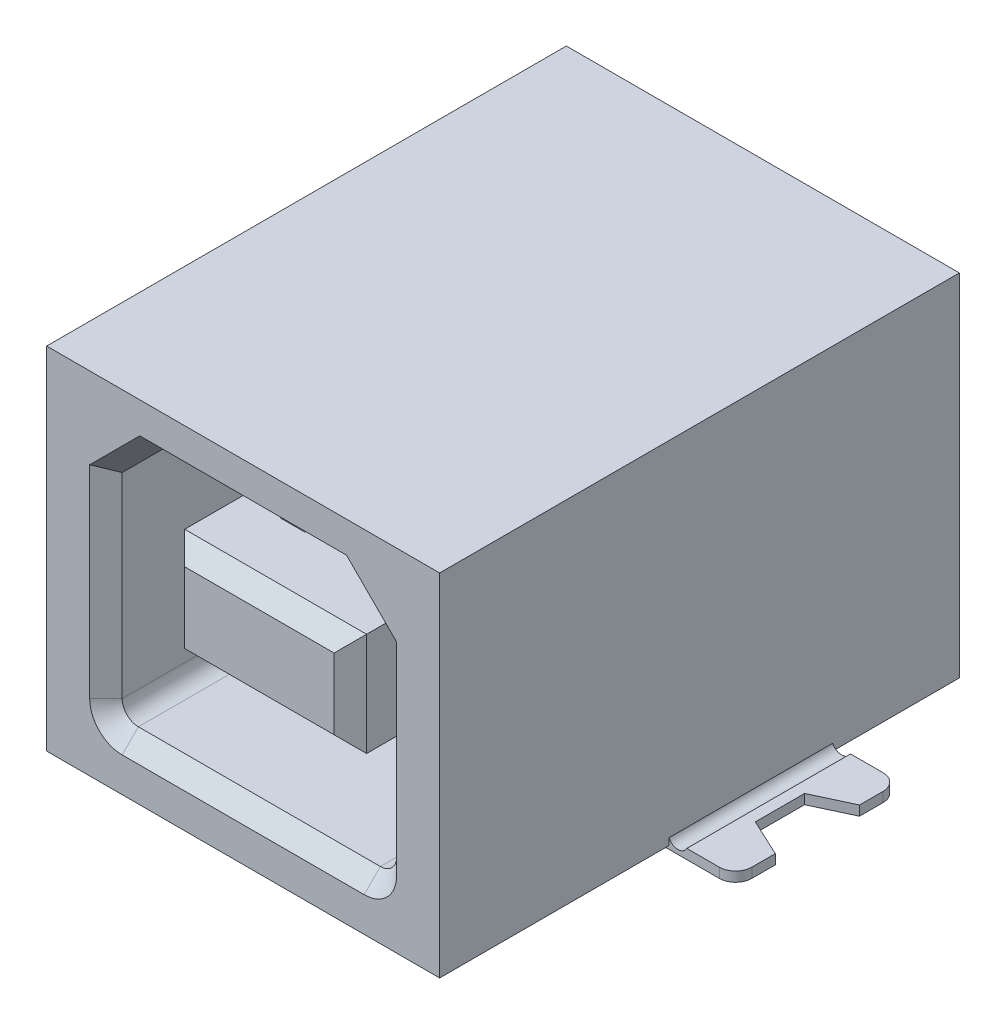
SolidWorks part; units mm, degrees
ref_plane "Front" through (0, 0, 0) normal (0, 0, 1) x (1, 0, 0)
ref_plane "Top" through (0, 0, 0) normal (0, 1, 0) x (1, 0, 0)
ref_plane "Right" through (0, 0, 0) normal (1, 0, 0) x (0, 0, -1)
sketch "Sketch1" plane through (0, 0, 0) normal (0, 0, 1) x (1, 0, 0)
  line L0 (-6.05, 5.4) -> (6.05, -5.4) construction
  line L1 (-6.05, 5.4) -> (6.05, 5.4)
  line L2 (-6.05, 5.4) -> (-6.05, -5.4)
  line L3 (-6.05, -5.4) -> (6.05, -5.4)
  line L4 (6.05, 5.4) -> (6.05, -5.4)
  dimension "D1" = 12.1
  dimension "D2" = 10.8
extrude "Base" add sketch "Sketch1" along normal mid plane 16
sketch "Sketch2" plane through (0, 0, 8) normal (0, 0, 1) x (1, 0, 0)
  line L0 (-2.975, 3.94) -> (-4.225, 2.69)
  line L1 (3.725, -3.84) -> (-3.725, -3.84)
  line L2 (4.225, -3.34) -> (4.225, 2.69)
  line L3 (2.975, 3.94) -> (-2.975, 3.94)
  line L4 (-4.225, -3.34) -> (-4.225, 2.69)
  line L5 (4.225, 2.69) -> (2.975, 3.94)
  line L6 (4.225, 3.94) -> (-4.225, -3.84) construction
  line L7 (6.05, 5.4) -> (-6.05, 5.4) construction
  line L9 (0, 0.05) -> (13.9883, 0.05) construction
  arc A0 (-3.725, -3.84) -> (-4.225, -3.34) centre (-3.725, -3.34) cw
  arc A1 (3.725, -3.84) -> (4.225, -3.34) centre (3.725, -3.34) ccw
  point P1 (4.225, 3.94)
  point P2 (-4.225, 3.94)
  point P12 (-4.225, -3.84)
  dimension "D1" = 0.5
  dimension "D2" = 5.35
  dimension "D3" = 8.45
  dimension "D5" = 7.78
extrude "Contact Opening" cut sketch "Sketch2" against normal blind 9
chamfer "Contact Opening Lead-in" distance 0.5 angle 45 8 edges at (-3.6, 3.315, 8) (0, 3.94, 8) (3.6, 3.315, 8) (4.225, -0.325, 8) (4.0786, -3.6936, 8) (0, -3.84, 8) (-4.0786, -3.6936, 8) (-4.225, -0.325, 8)
sketch "Sketch3" plane through (0, 0, -1) normal (0, 0, 1) x (1, 0, 0)
  line L0 (-2.8, 1.64) -> (2.8, -1.54) construction
  line L1 (-2.8, 1.64) -> (2.8, 1.64)
  line L2 (-2.8, 1.64) -> (-2.8, -1.54)
  line L3 (-2.8, -1.54) -> (2.8, -1.54)
  line L4 (2.8, 1.64) -> (2.8, -1.54)
  line L5 (-2.8, 0.05) -> (2.8, 0.05) construction
  line L6 (6.05, 5.4) -> (-6.05, 5.4) construction
  dimension "D1" = 5.6
  dimension "D2" = 3.18
  dimension "D3" = 5.35
extrude "Contact Area" add sketch "Sketch3" along normal blind 8.5
chamfer "Contact Area Lead-in" distance 0.5 angle 45 4 edges at (0, 1.64, 7.5) (2.8, 0.05, 7.5) (0, -1.54, 7.5) (-2.8, 0.05, 7.5)
ref_plane "Ground Leg Plane" through (0, 0, -1.58) normal (0, 0, 1) x (1, 0, 0)
sketch "Sketch4" plane through (0, 0, -1.58) normal (0, 0, 1) x (1, 0, 0)
  line L0 (0, 0) -> (0, -12.5407) construction
  line L1 (6.02, -5.058) -> (5.72, -5.1007)
  line L2 (6.5995, -5.2) -> (8.1, -5.2)
  line L3 (8.1, -5.2) -> (8.1, -5.5)
  line L5 (-5.9087, -5.5) -> (-8.1, -5.5)
  line L6 (-8.1, -5.2) -> (-8.1, -5.5)
  line L7 (-6.5995, -5.2) -> (-8.1, -5.2)
  line L8 (-6.02, -5.058) -> (-5.72, -5.1007)
  line L9 (5.9087, -5.5) -> (8.1, -5.5)
  arc A0 (6.02, -5.058) -> (6.5995, -5.2) centre (6.3271, -5.058) ccw
  arc A1 (-5.72, -5.1007) -> (-5.9087, -5.5) centre (-6.3271, -5.058) cw
  arc A2 (-6.02, -5.058) -> (-6.5995, -5.2) centre (-6.3271, -5.058) cw
  arc A5 (5.72, -5.1007) -> (5.9087, -5.5) centre (6.3271, -5.058) ccw
  dimension "D2" = 8.1
  dimension "D3" = 0.3
  dimension "D1" = 10.6
extrude "Ground Legs" add sketch "Sketch4" along normal mid plane 5.04
sketch "Sketch9" plane through (0, -5.2, 0) normal (0, 1, 0) x (-1, 0, 0)
  line L0 (-8.1, -4.1) -> (-8.1, -3.6)
  line L2 (-8.1, -4.1) -> (-7.6, -4.1)
  line L4 (0, -1.58) -> (-12.8295, -1.58) construction
  line L5 (-8.1, -2.8759) -> (-6.9467, -2.3383)
  line L6 (-8.1, 0.94) -> (-8.1, -4.1) construction
  line L7 (-6.9467, -2.3383) -> (-6.9467, -0.8217)
  line L8 (-8.1, -2.8759) -> (-8.1, -0.2841)
  line L9 (-8.1, -0.2841) -> (-6.9467, -0.8217)
  line L10 (-8.1, 0.94) -> (-7.6, 0.94)
  line L11 (-8.1, 0.94) -> (-8.1, 0.44)
  line L12 (6.321, -1.58) -> (-6.321, -1.58) construction
  line L13 (0, 0) -> (0, 10.0194) construction
  line L14 (8.1, 0.94) -> (8.1, 0.44)
  line L15 (8.1, 0.94) -> (7.6, 0.94)
  line L16 (8.1, -0.2841) -> (6.9467, -0.8217)
  line L17 (8.1, -2.8759) -> (8.1, -0.2841)
  line L18 (6.9467, -2.3383) -> (6.9467, -0.8217)
  line L19 (8.1, -2.8759) -> (6.9467, -2.3383)
  line L20 (8.1, -4.1) -> (7.6, -4.1)
  line L21 (8.1, -4.1) -> (8.1, -3.6)
  arc A0 (-8.1, -3.6) -> (-7.6, -4.1) centre (-7.6, -3.6) ccw
  arc A1 (-8.1, 0.44) -> (-7.6, 0.94) centre (-7.6, 0.44) cw
  arc A2 (8.1, 0.44) -> (7.6, 0.94) centre (7.6, 0.44) ccw
  arc A3 (8.1, -3.6) -> (7.6, -4.1) centre (7.6, -3.6) cw
  point P10 (-8.1, -4.1)
  point P17 (-8.1, 0.94)
  point P19 (-8.1, -1.58)
  point P20 (-6.9467, -1.58)
  point P32 (6.9467, -1.58)
  point P33 (8.1, -1.58)
  point P34 (8.1, 0.94)
  point P35 (8.1, -4.1)
  dimension "D1" = 0.5
  dimension "D2" = 0.5
  dimension "D3" = 1.2959
  dimension "D4" = 0.7583
extrude "ground legs shape" cut sketch "Sketch9" against normal blind 0.3
ref_plane "Tail Plane" through (0, 0, -6.9) normal (0, 0, -1) x (-1, 0, 0)
ref_plane "Contact Plane" through (-1.25, 0, 0) normal (1, 0, 0) x (0, 0, -1)
ref_plane "SM TAILS PLANE" through (0.75, 0, 0) normal (1, 0, 0) x (0, 0, -1)
sketch "Sketch11" plane through (0.75, 0, 0) normal (1, 0, 0) x (0, 0, -1)
  line L1 (7.15, -5.3) -> (7.15, -5.15)
  line L2 (7.15, -5.15) -> (7.4, -5.15)
  line L3 (8, -5.4) -> (8, 5.4) construction
  line L4 (4.1, -5.4) -> (8, -5.4) construction
  line L5 (-0.94, -5.5) -> (4.1, -5.5) construction
  line L6 (7.5, -5.25) -> (9.15, -5.25)
  line L8 (7.35, -5.5) -> (9.15, -5.5)
  line L9 (9.15, -5.25) -> (9.15, -5.5)
  arc A0 (7.4, -5.15) -> (7.5, -5.25) centre (7.5, -5.15) ccw
  arc A1 (7.15, -5.3) -> (7.35, -5.5) centre (7.35, -5.3) ccw
  dimension "D2" = 0.1
  dimension "D3" = 1.15
  dimension "D6" = 0.2
  dimension "D1" = 0.25
  dimension "D4" = 0.25
  dimension "D5" = 0.15
  dimension "D7" = 0.25
  dimension "D8" = 0.85
extrude "SM Tails" add sketch "Sketch11" along normal mid plane 0.6
sketch "Sketch8" plane through (-1.25, 0, 0) normal (1, 0, 0) x (0, 0, -1)
  line L0 (1, 1.64) -> (-2.5111, 2.2199)
  line L1 (-4.0305, 2.0775) -> (-5.5, 1.54)
  line L2 (-7, 1.64) -> (1, 1.64) construction
  line L3 (1, 2.69) -> (1, -3.34) construction
  line L4 (-3.9704, 1.9131) -> (-5.4399, 1.3756)
  line L5 (0.9715, 1.4673) -> (-2.5397, 2.0472)
  line L6 (0.9715, 1.4673) -> (1, 1.64)
  line L7 (-5.4399, 1.3756) -> (-5.5, 1.54)
  line L8 (1, 1.64) -> (1, -1.54) construction
  line L9 (1, 0.05) -> (-6.7483, 0.05) construction
  line L10 (-5.4399, -1.2756) -> (-5.5, -1.44)
  line L11 (0.9715, -1.3673) -> (1, -1.54)
  line L12 (0.9715, -1.3673) -> (-2.5397, -1.9472)
  line L13 (-3.9704, -1.8131) -> (-5.4399, -1.2756)
  line L14 (-4.0305, -1.9775) -> (-5.5, -1.44)
  line L15 (1, -1.54) -> (-2.5111, -2.1199)
  line L16 (-7, 1.64) -> (1, 1.64) construction
  arc A0 (-2.5111, 2.2199) -> (-4.0305, 2.0775) centre (-3, -0.74) ccw
  arc A1 (-2.5397, 2.0472) -> (-3.9704, 1.9131) centre (-3, -0.74) ccw
  arc A2 (-2.5397, -1.9472) -> (-3.9704, -1.8131) centre (-3, 0.84) cw
  arc A3 (-2.5111, -2.1199) -> (-4.0305, -1.9775) centre (-3, 0.84) cw
  point P26 (-3, 2.26)
  point P29 (-3, -2.16)
  dimension "D2" = 3
  dimension "D3" = 0.62
  dimension "D4" = 4
  dimension "D1" = 6.5
  dimension "D5" = 0.1
  dimension "D7" = 0.62
  dimension "D6" = 0.175
extrude "Contact" add sketch "Sketch8" along normal mid plane 0.75
pattern_linear "Contact Pattern" count 2 spacing 2.5 along (1, 0, 0) of "Contact"
pattern_linear "LPattern1" count 2 spacing 1.25 along (1, 0, 0) count 3 spacing 1.25 along (-1, 0, 0) of "SM Tails"
sketch "Sketch12" plane through (0, -5.4, 0) normal (0, -1, 0) x (1, 0, 0)
  line L0 (0, 0) -> (0, 5.4435) construction
  line L1 (3.1821, 8) -> (4.725, 8) construction
  circle A0 centre (2.75, -1) radius 0.575
  circle A1 centre (-2.75, -1) radius 0.575
  point P5 (3.9536, 8)
  dimension "D1" = 1.15
  dimension "D2" = 2.75
  dimension "D3" = 9
extrude "Alignment Pin" add sketch "Sketch12" along normal blind 1.9
chamfer "Pin Point" distance 0.05 2 edges at (2.75, -7.3, -1.575) (-2.75, -7.3, -0.425)
sketch "Sketch15" plane through (0, 0, -6.9) normal (0, 0, -1) x (-1, 0, 0)
  line L0 (-1.55, -5.4) -> (-0.95, -5.4)
  line L1 (-1.55, -5.4) -> (-1.55, -8.2)
  line L2 (-1.4288, -8.5) -> (-1.0712, -8.5)
  line L3 (-0.95, -5.4) -> (-0.95, -8.2)
  line L4 (-1.55, -8.2) -> (-1.4288, -8.5)
  line L5 (-0.95, -8.2) -> (-1.0712, -8.5)
  line L6 (1.25, -5.4) -> (1.25, -8.4) construction
  line L7 (0.95, -8.2) -> (1.0712, -8.5)
  line L8 (1.55, -8.2) -> (1.4288, -8.5)
  line L9 (0.95, -5.4) -> (0.95, -8.2)
  line L10 (1.4288, -8.5) -> (1.0712, -8.5)
  line L11 (1.55, -5.4) -> (1.55, -8.2)
  line L12 (1.55, -5.4) -> (0.95, -5.4)
  line L14 (0, 0) -> (0, -9.474) construction
  line L15 (6.05, -5.4) -> (2.05, -5.4) construction
  point P14 (-1.25, -5.4)
  dimension "D1" = 0.3
  dimension "D2" = 0.6
  dimension "D3" = 1.25
  dimension "D4" = 0.1212
  dimension "D5" = 3.1
  dimension "D6" = 0.1212
  dimension "D7" = 2.5
ref_plane "VT Plane" [suppressed] through (0, -0.9, 0) normal (0, -1, 0) x (-1, 0, 0)
sketch "Sketch18" plane through (0, 0, -8) normal (0, 0, -1) x (-1, 0, 0)
  line L0 (1.61, -1.34) -> (0.99, -1.34) construction
  line L1 (1.61, -1.465) -> (0.99, -1.465)
  line L2 (1.61, -1.465) -> (1.61, -1.215)
  line L3 (1.61, -1.215) -> (0.99, -1.215)
  line L4 (0.99, -1.465) -> (0.99, -1.215)
  line L5 (6.05, -5.4) -> (2.05, -5.4) construction
  line L6 (1.3, -1.465) -> (1.3, -1.215) construction
  line L7 (6.05, 5.4) -> (6.05, -5.4) construction
  line L8 (-0.89, -1.465) -> (-1.51, -1.465)
  line L9 (-0.89, -1.465) -> (-0.89, -1.215)
  line L10 (-0.89, -1.215) -> (-1.51, -1.215)
  line L11 (-1.51, -1.465) -> (-1.51, -1.215)
  line L12 (-0.89, 1.735) -> (-1.51, 1.735)
  line L13 (-0.89, 1.735) -> (-0.89, 1.985)
  line L14 (-0.89, 1.985) -> (-1.51, 1.985)
  line L15 (-1.51, 1.735) -> (-1.51, 1.985)
  line L16 (1.61, 1.735) -> (0.99, 1.735)
  line L17 (1.61, 1.735) -> (1.61, 1.985)
  line L18 (1.61, 1.985) -> (0.99, 1.985)
  line L19 (0.99, 1.735) -> (0.99, 1.985)
  dimension "D1" = 0.62
  dimension "D2" = 0.25
  dimension "D3" = 4.06
  dimension "D4" = 4.75
  dimension "D5" = 2
  dimension "D6" = 2
